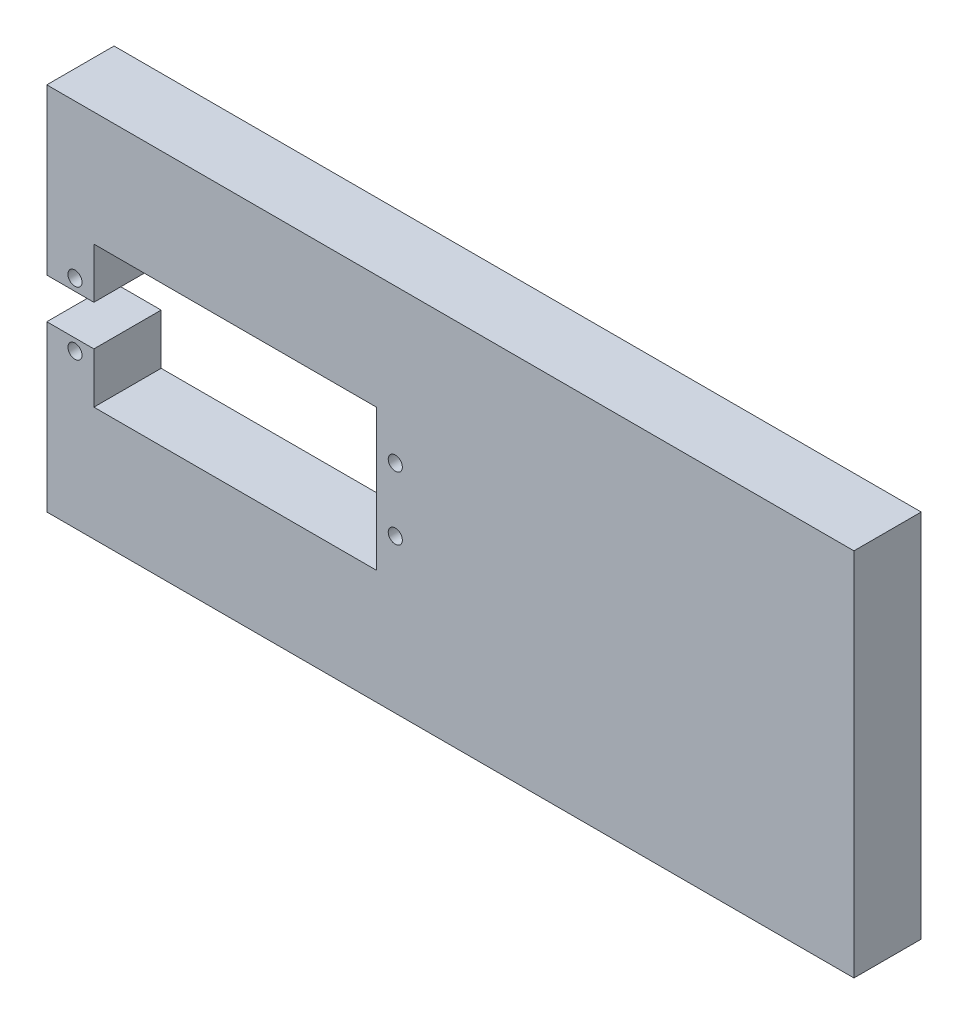
SolidWorks part; units mm, degrees
ref_plane "前基準面" through (0, 0, 0) normal (0, 0, 1) x (1, 0, 0)
ref_plane "上基準面" through (0, 0, 0) normal (0, 1, 0) x (1, 0, 0)
ref_plane "右基準面" through (0, 0, 0) normal (1, 0, 0) x (0, 0, -1)
sketch "草圖1" plane through (0, 0, 0) normal (0, 0, 1) x (1, 0, 0)
  line L0 (0, -55) -> (0, 55) construction
  line L1 (-60, 27.5) -> (60, 27.5)
  line L2 (-60, 27.5) -> (-60, 3)
  line L3 (-60, -27.5) -> (60, -27.5)
  line L4 (60, 27.5) -> (60, -27.5)
  line L5 (55, 0) -> (-55, 0) construction
  line L6 (-53, -3) -> (-53, -10.5)
  line L7 (-53, 10.5) -> (-11, 10.5)
  line L8 (-53, 10.5) -> (-53, 3)
  line L9 (-53, -10.5) -> (-11, -10.5)
  line L10 (-11, 10.5) -> (-11, -10.5)
  line L11 (-60, 3) -> (-53, 3)
  line L13 (-60, -3) -> (-53, -3)
  line L15 (-60, -3) -> (-60, -27.5)
  circle A0 centre (-55.81, 4.7) radius 1.05
  circle A1 centre (-8.19, 4.7) radius 1.05
  circle A2 centre (-55.81, -4.7) radius 1.05
  circle A3 centre (-8.19, -4.7) radius 1.05
  dimension "D1" = 120
  dimension "D2" = 60
  dimension "D3" = 55
  dimension "D4" = 27.5
  dimension "D5" = 42
  dimension "D6" = 21
  dimension "D7" = 10.5
  dimension "D8" = 7
  dimension "D9" = 6
  dimension "D10" = 3
  dimension "D11" = 2.81
  dimension "D12" = 5.8
  dimension "D13" = 5.8
  dimension "D14" = 2.81
extrude "填料-伸長1" add sketch "草圖1" along normal blind 10
